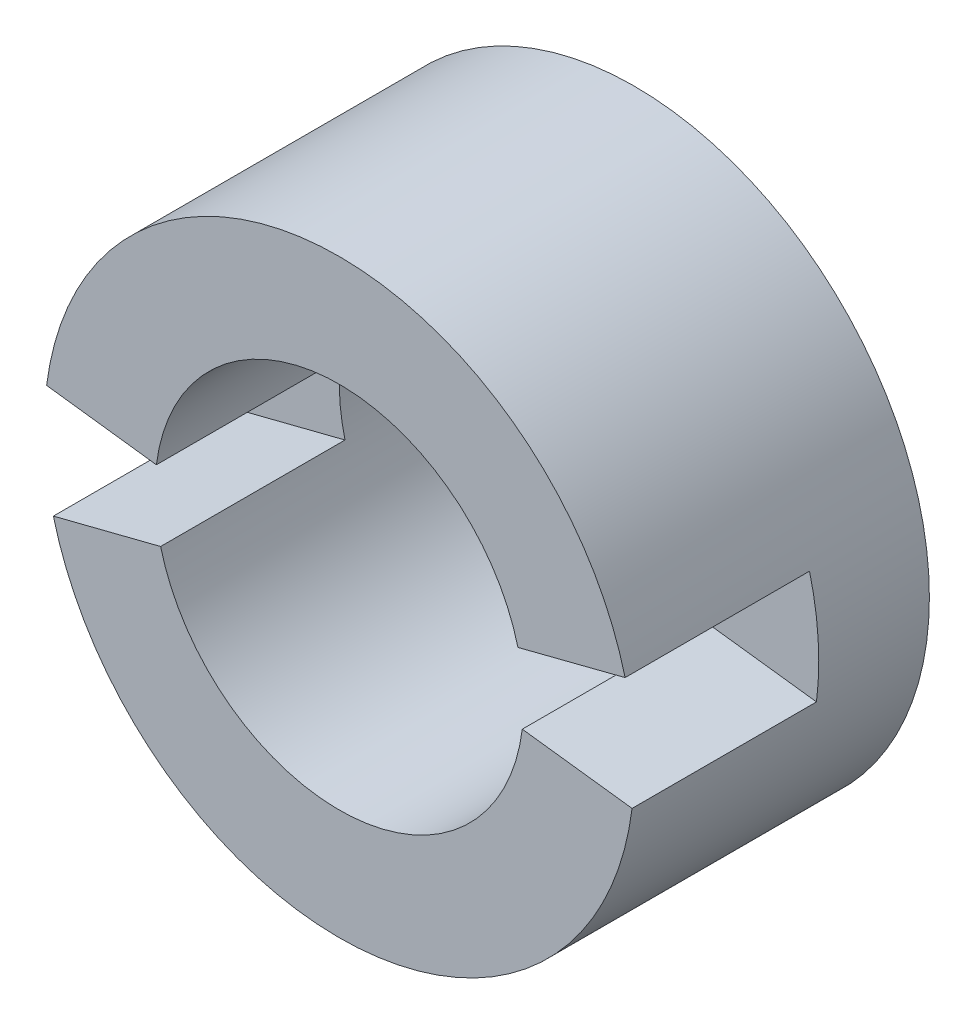
SolidWorks part; units mm, degrees
ref_plane "Front Plane" through (0, 0, 0) normal (0, 0, 1) x (1, 0, 0)
ref_plane "Top Plane" through (0, 0, 0) normal (0, 1, 0) x (1, 0, 0)
ref_plane "Right Plane" through (0, 0, 0) normal (1, 0, 0) x (0, 0, -1)
sketch "Sketch1" plane through (0, 0, 0) normal (0, 0, 1) x (1, 0, 0)
  circle A0 centre (0, 0) radius 5
  circle A1 centre (0, 0) radius 8
  dimension "D1" = 10
  dimension "D2" = 16
extrude "Boss-Extrude1" add sketch "Sketch1" along normal blind 8
sketch "Sketch2" plane through (0, 0, 0) normal (0, 1, 0) x (1, 0, 0)
  line L0 (10.56, -3) -> (13.56, -3)
  line L1 (10.56, -8) -> (10.56, -3)
  line L2 (-11.56, -8) -> (-11.56, -3)
  line L3 (-11.56, -3) -> (-14.56, -3)
  line L4 (-14.56, -3) -> (-14.56, -8)
  line L5 (-14.56, -8) -> (-11.56, -8)
  line L6 (13.56, -3) -> (13.56, -8)
  line L7 (13.56, -8) -> (10.56, -8)
  dimension "D1" = 5
  dimension "D2" = 10.56
  dimension "D3" = 11.56
  dimension "D4" = 3
  dimension "D5" = 3
  dimension "D6" = 3
wrap "Wrap2" sketch "Sketch2" wrap type deboss source sketch "Sketch2" thickness 4 face at (8, 0, 8) parameters "D1"=4
